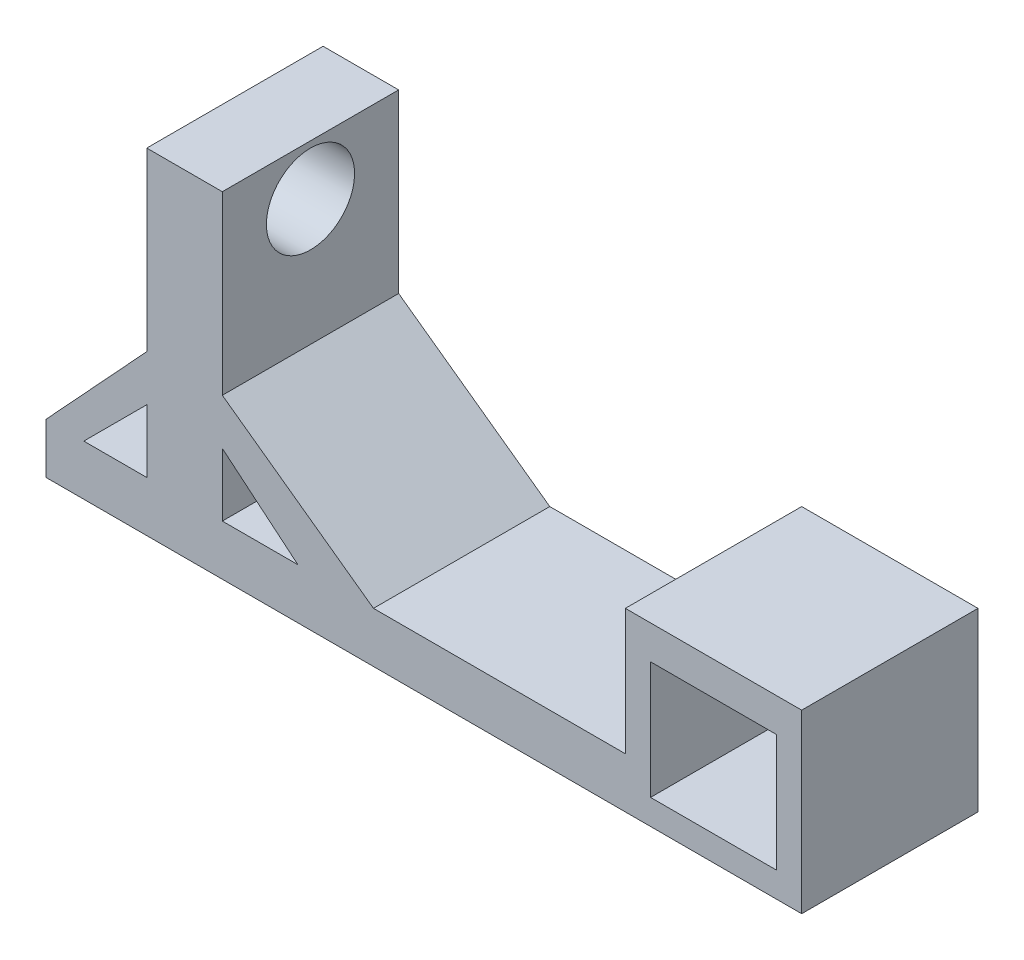
SolidWorks part; units mm, degrees
ref_plane "前视基准面" through (0, 0, 0) normal (0, 0, 1) x (1, 0, 0)
ref_plane "上视基准面" through (0, 0, 0) normal (0, 1, 0) x (1, 0, 0)
ref_plane "右视基准面" through (0, 0, 0) normal (1, 0, 0) x (0, 0, -1)
sketch "草图1" plane through (0, 0, 0) normal (0, 0, 1) x (1, 0, 0)
  line L0 (-65.25, 63.25) -> (-65.25, -6.75)
  line L1 (-65.25, -6.75) -> (-105.25, -50)
  line L2 (-105.25, -50) -> (-105.25, -70)
  line L3 (-105.25, -70) -> (194.75, -70)
  line L4 (194.75, -70) -> (194.75, 0)
  line L5 (194.75, 0) -> (124.75, 0)
  line L6 (124.75, 0) -> (124.75, -50)
  line L7 (124.75, -50) -> (24.75, -50)
  line L8 (24.75, -50) -> (-35.25, -6.75)
  line L9 (-35.25, -6.75) -> (-35.25, 63.25)
  line L10 (-65.25, 63.25) -> (-35.25, 63.25)
  point P11 (-35.25, 28.25)
  point P13 (0, 0)
  dimension "D1" = 30
  dimension "D2" = 70
  dimension "D3" = 70
  dimension "D4" = 20
  dimension "D5" = 70
  dimension "D6" = 70
  dimension "D7" = 100
  dimension "D8" = 300
  dimension "D9" = 70
  dimension "D10" = 50
extrude "凸台-拉伸1" add sketch "草图1" along normal blind 70
sketch "草图2" plane through (0, 0, 70) normal (0, 0, 1) x (1, 0, 0)
  line L0 (134.75, -13.3762) -> (134.75, -60)
  line L1 (134.75, -60) -> (184.75, -60)
  line L2 (184.75, -60) -> (184.75, -13.3762)
  line L3 (184.75, -13.3762) -> (134.75, -13.3762)
  line L5 (-105.25, -70) -> (194.75, -70) construction
  line L6 (194.75, -70) -> (194.75, 0) construction
  dimension "D1" = 50
  dimension "D2" = 46.6238
  dimension "D3" = 10
  dimension "D4" = 10
extrude "切除-拉伸1" cut sketch "草图2" against normal blind 70
sketch "草图3" plane through (-35.25, 0, 0) normal (1, 0, 0) x (0, 0, -1)
  line L0 (-70, -6.75) -> (-70, 63.25) construction
  line L1 (-70, 63.25) -> (0, 63.25) construction
  circle A0 centre (-35, 43.25) radius 17.5
  point P4 (0, 0)
  point P5 (0, 0)
  point P6 (-49.8925, 55.4709)
  point P10 (-24.6393, 33.2199)
  dimension "D3" = 35
  dimension "D1" = 35
  dimension "D2" = 20
extrude "切除-拉伸2" cut sketch "草图3" against normal up to next
sketch "草图4" plane through (0, 0, 70) normal (0, 0, 1) x (1, 0, 0)
  line L0 (-65.25, -25) -> (-90.25, -50)
  line L1 (-90.25, -50) -> (-65.25, -50)
  line L2 (-65.25, -50) -> (-65.25, -25)
  line L3 (-35.25, -25) -> (-35.25, -50)
  line L4 (-35.25, -50) -> (-5.25, -50)
  line L5 (-5.25, -50) -> (-35.25, -25)
  line L6 (-35.25, -6.75) -> (-35.25, 63.25) construction
  line L7 (-65.25, 63.25) -> (-65.25, -6.75) construction
  line L8 (124.75, -50) -> (24.75, -50) construction
  dimension "D1" = 25
  dimension "D2" = 25
  dimension "D3" = 30
  dimension "D4" = 25
extrude "切除-拉伸3" cut sketch "草图4" against normal blind 70
